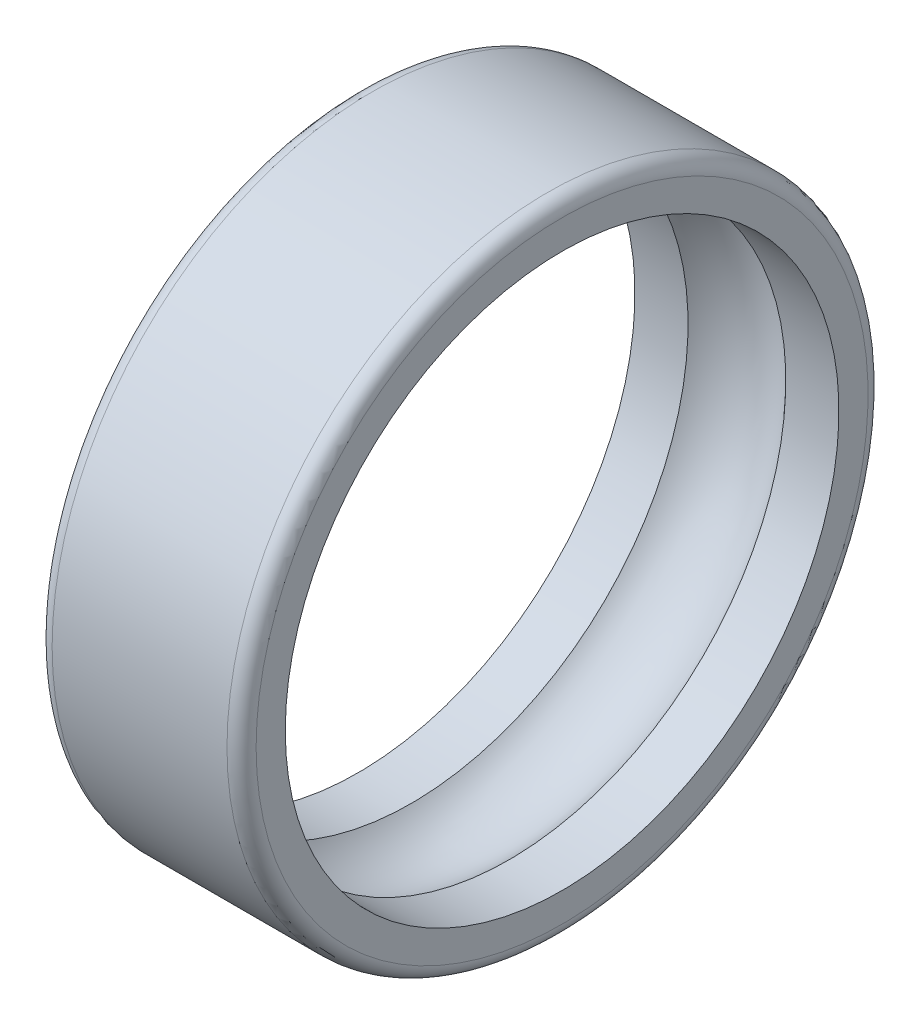
SolidWorks part; units mm, degrees
material "Chrome Stainless Steel"
ref_plane "Front Plane" through (0, 0, 0) normal (0, 0, 1) x (1, 0, 0)
ref_plane "Top Plane" through (0, 0, 0) normal (0, 1, 0) x (1, 0, 0)
ref_plane "Right Plane" through (0, 0, 0) normal (1, 0, 0) x (0, 0, -1)
sketch "Sketch1" plane through (0, 0, 0) normal (0, 0, 1) x (1, 0, 0)
  line L0 (-29.8426, 0) -> (39.3148, 0) construction
  line L1 (0, -2.0587) -> (0, 14.3228) construction
  line L2 (-3.5, 9.5) -> (-1.6771, 9.5)
  line L3 (-3.5, 9.5) -> (-3.5, 11)
  line L4 (-3.5, 11) -> (3.5, 11)
  line L5 (3.5, 9.5) -> (3.5, 11)
  line L6 (1.6771, 9.5) -> (3.5, 9.5)
  arc A0 (-1.6771, 9.5) -> (1.6771, 9.5) centre (0, 8) cw
  dimension "D6" = 2.25
  dimension "D1" = 7
  dimension "D2" = 11
  dimension "D3" = 1.5
  dimension "D4" = 3.5
  dimension "D5" = 8
revolve "Revolve1" add sketch "Sketch1" angle 360 about L0
fillet "Fillet1" radius 0.5 2 edges at (3.5, 0, 11) (-3.5, 0, 11)
